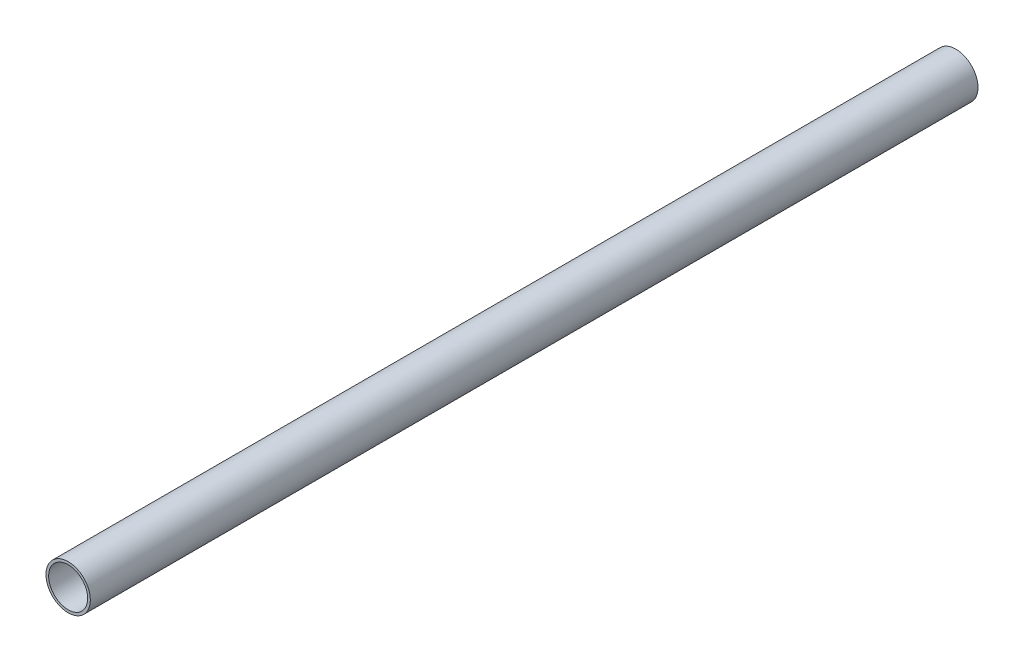
SolidWorks part; units mm, degrees
ref_plane "Plan de face" through (0, 0, 0) normal (0, 0, 1) x (1, 0, 0)
ref_plane "Plan de dessus" through (0, 0, 0) normal (0, 1, 0) x (1, 0, 0)
ref_plane "Plan de droite" through (0, 0, 0) normal (1, 0, 0) x (0, 0, -1)
sketch "Esquisse1" plane through (0, 0, 0) normal (0, 0, 1) x (1, 0, 0)
  circle A0 centre (0, 0) radius 22
  circle A1 centre (0, 0) radius 25
  dimension "D1" = 44
  dimension "D2" = 50
extrude "Boss.-Extru.1" add sketch "Esquisse1" along normal blind 1000
